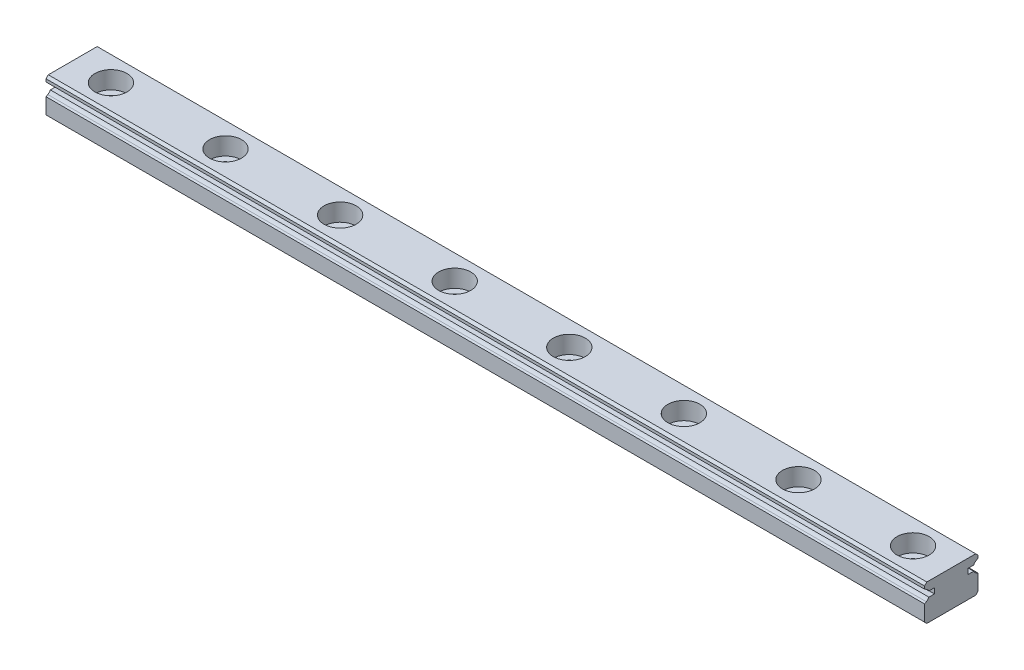
SolidWorks part; units mm, degrees
ref_plane "Front Plane" through (0, 0, 0) normal (0, 0, 1) x (1, 0, 0)
ref_plane "Top Plane" through (0, 0, 0) normal (0, 1, 0) x (1, 0, 0)
ref_plane "Right Plane" through (0, 0, 0) normal (1, 0, 0) x (0, 0, -1)
ref_plane "Plane1" through (-5, 0, 0) normal (1, 0, 0) x (0, 0, -1)
sketch "Sketch1" plane through (-5, 0, 0) normal (1, 0, 0) x (0, 0, -1)
  line L0 (0, 4.7) -> (0, 0) construction
  line L1 (-3.5, 4.7) -> (3.5, 4.7)
  line L3 (-3.5, 0) -> (3.5, 0)
  line L10 (3.5, 4.7) -> (3.5, 0)
  line L11 (-3.5, 4.7) -> (-3.5, 0)
  dimension "H1" = 4.7
  dimension "W1" = 7
extrude "Boss-Extrude1" add sketch "Sketch1" along normal blind 115
sketch "Sketch2" plane through (-5, 0, 0) normal (1, 0, 0) x (0, 0, -1)
  line L0 (2.2, 3.2) -> (3.5, 3.2) construction
  line L1 (0, 0) -> (0, 3.55) construction
  line L2 (3.5, 4.0349) -> (3.27, 3.9021)
  line L3 (2.2, 3.55) -> (2.9313, 3.55)
  line L4 (2.2, 3.55) -> (2.2, 2.85)
  line L5 (2.2, 2.85) -> (2.9313, 2.85)
  line L6 (3.5, 2.3651) -> (3.27, 2.4979)
  line L7 (3.5, 4.7) -> (3.5, 0) construction
  line L8 (3.5, 4.0349) -> (3.5, 2.3651)
  line L9 (-3.5, 0) -> (3.5, 0) construction
  line L10 (-2.2, 3.2) -> (-3.5, 3.2) construction
  line L11 (-3.5, 4.0349) -> (-3.5, 2.3651)
  line L12 (-3.5, 2.3651) -> (-3.27, 2.4979)
  line L13 (-2.2, 2.85) -> (-2.9313, 2.85)
  line L14 (-2.2, 3.55) -> (-2.2, 2.85)
  line L15 (-2.2, 3.55) -> (-2.9313, 3.55)
  line L16 (-3.5, 4.0349) -> (-3.27, 3.9021)
  arc A0 (3.27, 3.9021) -> (2.9313, 3.55) centre (3.71, 3.14) ccw
  arc A1 (2.9313, 2.85) -> (3.27, 2.4979) centre (3.71, 3.26) ccw
  arc A2 (-2.9313, 2.85) -> (-3.27, 2.4979) centre (-3.71, 3.26) cw
  arc A3 (-3.27, 3.9021) -> (-2.9313, 3.55) centre (-3.71, 3.14) cw
  dimension "MSM_8" = 0.88
  dimension "MSM_6" = 3.2
  dimension "MSM_7" = 60
  dimension "MSM_2" = 0.21
  dimension "MSM_5" = 0.7
  dimension "MSM_1" = 1.3
  dimension "MSM_3" = 3.26
  dimension "MSM_4" = 3.14
extrude "Cut-Extrude1" cut sketch "Sketch2" along normal through all
hole_wizard "CBORE for Socket Head Cap Screw1" positions "Sketch4" profile "Sketch3" counterbore size "M3" standard "JIS" end condition through all
sketch "Sketch4" plane through (0, 4.7, 0) normal (0, 1, 0) x (1, 0, 0)
  line L0 (-5, -3.025) -> (-5, 3.025) construction
  point P0 (0, 0)
  dimension "G" = 5
sketch "Sketch3" plane through (0, 4.7, 0) normal (1, 0, 0) x (0, 0, 1)
  line L0 (0, 0) -> (0, 4.7)
  line L1 (0, 4.7) -> (1.2, 4.7)
  line L3 (1.2, 4.7) -> (1.2, 2.3)
  line L4 (1.2, 2.3) -> (2.1, 2.3)
  line L5 (2.1, 2.3) -> (2.1, 0)
  line L7 (2.1, 0) -> (0, 0)
  line L11 (0, 0) -> (0, 4.7) construction
  dimension "D1_s" = 2.4
  dimension "Thru Hole Depth" = 4.7
  dimension "D2_s" = 4.2
  dimension "H_s" = 2.3
pattern_linear "LPattern1" count 8 spacing 15 along (1, 0, 0) of "CBORE for Socket Head Cap Screw1"
chamfer "Chamfer1" distance 0.3 2 edges at (52.5, 4.7, 3.5) (52.5, 4.7, -3.5)
chamfer "Chamfer2" distance 0.3 2 edges at (52.5, 0, -3.5) (52.5, 0, 3.5)
ref_plane "Plane2" [suppressed] through (0, 5.5, 0) normal (0, 1, 0) x (1, 0, 0)
hole_wizard "Tap1" [suppressed] positions "Sketch6" profile "Sketch5" hole size "M3x0.5" standard "JIS"
sketch "Sketch6" [suppressed] plane through (0, 5.5, 0) normal (0, 1, 0) x (1, 0, 0)
  line L0 (-7.5, -3.025) -> (-7.5, 3.025) construction
  point P0 (0, 0)
  dimension "G" = 5
sketch "Sketch5" [suppressed] plane through (0, 5.5, 0) normal (1, 0, 0) x (0, 0, 1)
  line L0 (0, 0) -> (0, 5.5)
  line L1 (0, 5.5) -> (1.621, 5.5)
  line L2 (1.621, 5.5) -> (1.621, 0)
  line L5 (1.621, 0) -> (0, 0)
  line L11 (0, 0) -> (0, 5.5) construction
  dimension "STD_1" = 3.242
  dimension "Thru Hole Depth" = 5.5
cosmetic thread "Thread1" [suppressed] parameters "MC"=4
pattern_linear "LPattern2" [suppressed]
sketch "Sketch7" [suppressed] plane through (0, 0, 0) normal (0, 0, 1) x (1, 0, 0)
  line L0 (0, 5.5) -> (0, 0) construction
  line L1 (-7.5, 5.5) -> (-5, 5.5)
  line L2 (-7.5, 5.5) -> (-7.5, 0)
  line L3 (-7.5, 0) -> (-5, 0)
  line L4 (-5, 5.5) -> (-5, 0)
  line L5 (-7.5, -3.025) -> (-7.5, 3.025) construction
  dimension "LLC" = 2.5
  dimension "N" = 5
extrude "Cut-Extrude2" [suppressed] cut sketch "Sketch7" against normal through all and the other way through all
sketch "Sketch8" [suppressed] plane through (0, 0, 0) normal (0, 0, 1) x (1, 0, 0)
  line L0 (22.5, 5.5) -> (22.5, 0) construction
  line L1 (25, 5.5) -> (27.5, 5.5)
  line L2 (25, 5.5) -> (25, 0)
  line L3 (25, 0) -> (27.5, 0)
  line L4 (27.5, 5.5) -> (27.5, 0)
  line L5 (-7.5, 5.5) -> (-7.5, 0)
  line L6 (-7.5, 5.5) -> (-7.5, 0) construction
  dimension "RLC" = 2.5
  dimension "N" = 2.5
  dimension "L" = 115
extrude "Cut-Extrude3" [suppressed] cut sketch "Sketch8" against normal through all and the other way through all contours L1 L4 L3 L2
